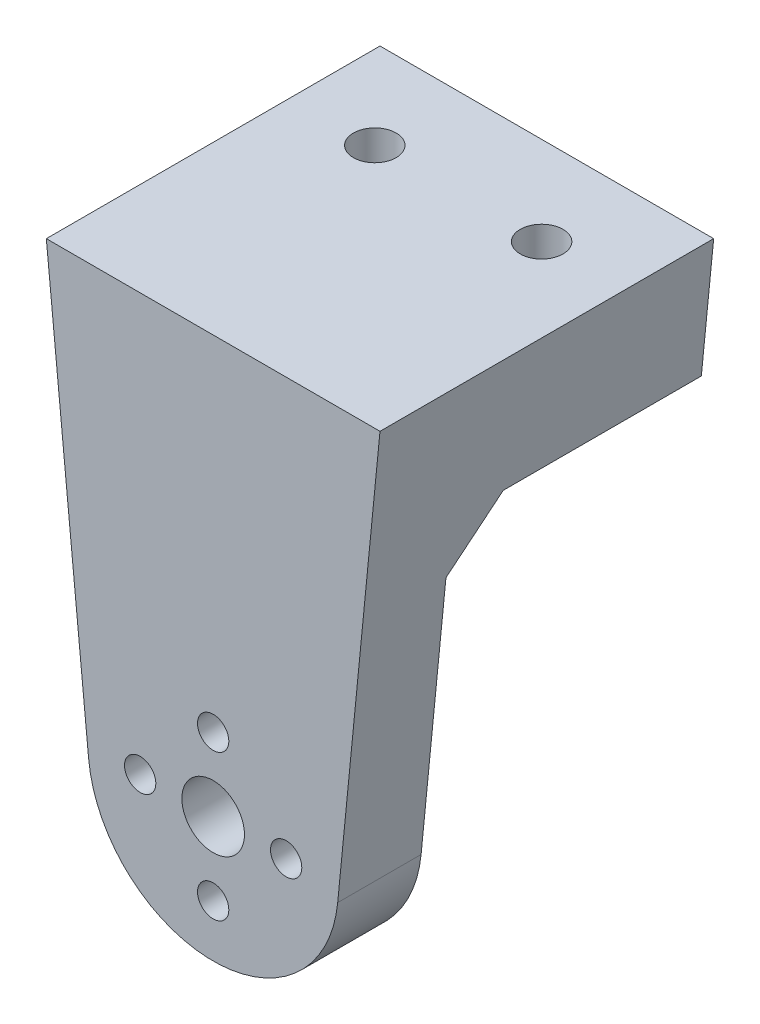
SolidWorks part; units mm, degrees
ref_plane "Front" through (0, 0, 0) normal (0, 0, 1) x (1, 0, 0)
ref_plane "Top" through (0, 0, 0) normal (0, 1, 0) x (1, 0, 0)
ref_plane "Right" through (0, 0, 0) normal (1, 0, 0) x (0, 0, -1)
sketch "Sketch1" plane through (0, 0, 0) normal (0, 0, 1) x (1, 0, 0)
  line L0 (-11.9422, -1.1769) -> (-16, 40)
  line L1 (-16, 40) -> (16, 40)
  line L2 (16, 40) -> (11.9422, -1.1769)
  line L3 (0, 40) -> (0, 0) construction
  circle A0 centre (0, 0) radius 12
  circle A1 centre (0, 7) radius 1.5
  circle A2 centre (7, 0) radius 1.5
  circle A3 centre (0, -7) radius 1.5
  circle A4 centre (-7, 0) radius 1.5
  point P19 (0, 0)
  dimension "D1" = 24
  dimension "D4" = 3
  dimension "D2" = 32
  dimension "D3" = 40
  dimension "D5" = 7
  dimension "D6" = 4
extrude "Boss-Extrude1" add sketch "Sketch1" along normal blind 8
sketch "Sketch3" plane through (0, 0, 0) normal (0, 0, -1) x (-1, 0, 0)
  line L3 (14.8174, 28) -> (-14.8174, 28)
  line L4 (16, 28) -> (-16, 28) construction
  line L6 (11.9422, -1.1769) -> (16, 40)
  line L7 (16, 40) -> (-16, 40)
  line L8 (-16, 40) -> (-11.9422, -1.1769)
  line L9 (14.8174, 28) -> (16, 40)
  line L10 (16, 40) -> (-16, 40)
  line L11 (-16, 40) -> (-14.8174, 28)
  arc A2 (-11.9422, -1.1769) -> (11.9422, -1.1769) centre (0, 0) ccw
  dimension "D1" = 0
  dimension "D2" = 12
extrude "Boss-Extrude2" add sketch "Sketch3" along normal blind 24
chamfer "Chamfer1" distance 5 angle 45 1 edges at (0, 28, 0)
sketch "Sketch5" plane through (0, 0, 0) normal (0, 0, -1) x (-1, 0, 0)
  circle A0 centre (0, 0) radius 3
  dimension "D1" = 6
extrude "Cut-Extrude2" cut sketch "Sketch5" against normal up to next
sketch "Sketch6" plane through (0, 40, 0) normal (0, -1, 0) x (1, 0, 0)
  line L14 (14.8174, -24) -> (-14.8174, -24) construction
  circle A2 centre (-8, -15.5) radius 2.05
  circle A3 centre (8, -15.5) radius 2.05
  dimension "D5" = 4.1
  dimension "D6" = 4.1
  dimension "D1" = 16
  dimension "D2" = 8
  dimension "D7" = 8.5
extrude "Cut-Extrude6" cut sketch "Sketch6" along normal blind 5 contours A2 | A3
